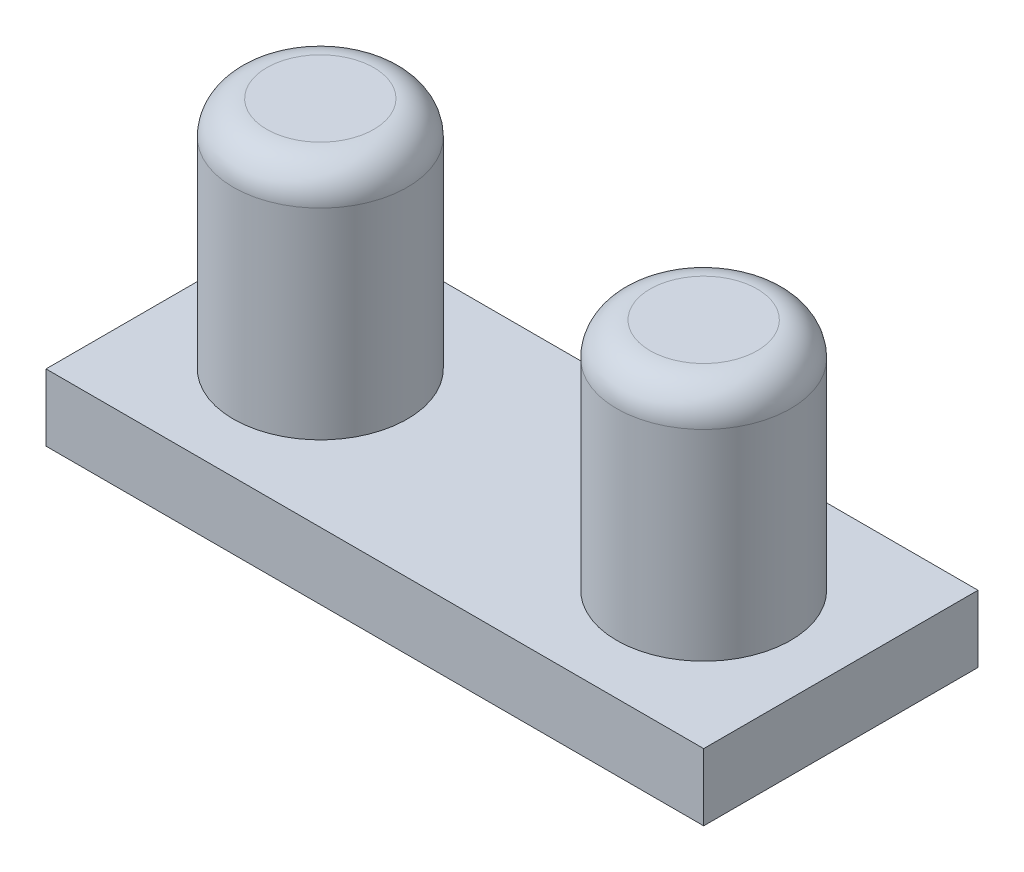
SolidWorks part; units mm, degrees
ref_plane "Front Plane" through (0, 0, 0) normal (0, 0, 1) x (1, 0, 0)
ref_plane "Top Plane" through (0, 0, 0) normal (0, 1, 0) x (1, 0, 0)
ref_plane "Right Plane" through (0, 0, 0) normal (1, 0, 0) x (0, 0, -1)
sketch "Sketch2" plane through (0, 0, 0) normal (0, 1, 0) x (1, 0, 0)
  line L1 (-9.83, 4.1) -> (9.83, 4.1)
  line L2 (-9.83, 4.1) -> (-9.83, -4.1)
  line L3 (-9.83, -4.1) -> (9.83, -4.1)
  line L4 (9.83, 4.1) -> (9.83, -4.1)
  line L5 (-9.83, 4.1) -> (9.83, -4.1) construction
  line L6 (-9.83, -4.1) -> (9.83, 4.1) construction
  point P0 (0, 0)
  dimension "D1" = 8.2
  dimension "D2" = 19.66
extrude "Boss-Extrude1" add sketch "Sketch2" along normal blind 2
sketch "Sketch3" plane through (0, 2, 0) normal (0, 1, 0) x (1, 0, 0)
  circle A0 centre (-5.73, 0) radius 2.6
  circle A1 centre (5.73, 0) radius 2.6
  dimension "D1" = 5.2
  dimension "D2" = 5.2
  dimension "D4" = 5.73
  dimension "D3" = 5.73
extrude "Boss-Extrude2" add sketch "Sketch3" along normal blind 7
fillet "Fillet1" radius 1 2 edges at (5.73, 9, 2.6) (-5.73, 9, 2.6)
